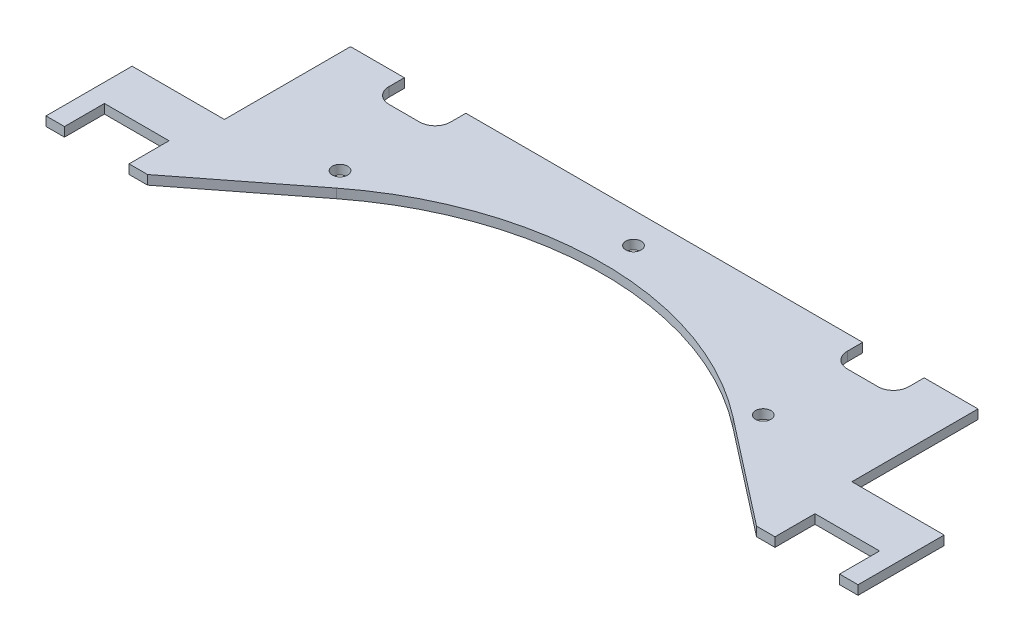
SolidWorks part; units mm, degrees
ref_plane "Face" through (0, 0, 0) normal (0, 0, 1) x (1, 0, 0)
ref_plane "Dessus" through (0, 0, 0) normal (0, 1, 0) x (1, 0, 0)
ref_plane "Droite" through (0, 0, 0) normal (1, 0, 0) x (0, 0, -1)
sketch "Esquisse1" plane through (0, 0, 0) normal (0, 1, 0) x (1, 0, 0)
  line L0 (0, 0) -> (0, 372.8366) construction
  line L1 (0, 0) -> (0, -232.7616) construction
  line L2 (558.5742, 0) -> (-497.8331, 0) construction
  line L3 (-64.4944, 52.8582) -> (-99, 26)
  line L4 (-132, 26) -> (-126, 26)
  line L5 (-132, 26) -> (-132, 54)
  line L6 (-132, 54) -> (-102, 54)
  line L7 (132, 26) -> (132, 54)
  line L8 (-132, 26) -> (-99, 26) construction
  line L9 (64.4944, 52.8582) -> (99, 26)
  line L10 (-79.5, 85) -> (-69.5, 85)
  line L11 (-84.5, 95) -> (-84.5, 90)
  line L12 (-64.5, 95) -> (-64.5, 90)
  line L13 (-64.5, 95) -> (64.5, 95)
  line L14 (-79.5, 90) -> (-69.5, 90) construction
  line L15 (84.5, 95) -> (84.5, 90)
  line L16 (102, 95) -> (84.5, 95)
  line L17 (79.5, 85) -> (69.5, 85)
  line L18 (-102, 54) -> (-102, 95)
  line L19 (-102, 95) -> (-84.5, 95)
  line L20 (-126, 26) -> (-126, 39)
  line L21 (-126, 39) -> (-105, 39)
  line L22 (-105, 39) -> (-105, 26)
  line L23 (-105, 26) -> (-99, 26)
  line L24 (-115.5, 26) -> (-115.5, 39) construction
  line L25 (132, 26) -> (126, 26)
  line L26 (126, 26) -> (126, 39)
  line L27 (126, 39) -> (105, 39)
  line L28 (105, 39) -> (105, 26)
  line L29 (105, 26) -> (99, 26)
  line L30 (132, 54) -> (102, 54)
  line L31 (102, 54) -> (102, 95)
  line L32 (-64.4944, 52.8582) -> (64.4944, 52.8582) construction
  line L33 (-64.4944, 52.8582) -> (-68.794, 58.382) construction
  line L34 (64.5, 95) -> (64.5, 90)
  arc A0 (64.4944, 52.8582) -> (-64.4944, 52.8582) centre (0, -30) ccw
  arc A1 (-84.5, 90) -> (-79.5, 85) centre (-79.5, 90) ccw
  arc A2 (-69.5, 85) -> (-64.5, 90) centre (-69.5, 90) ccw
  arc A3 (84.5, 90) -> (79.5, 85) centre (79.5, 90) cw
  arc A4 (69.5, 85) -> (64.5, 90) centre (69.5, 90) cw
  circle A11 centre (-68.794, 58.382) radius 2.5
  circle A12 centre (68.794, 58.382) radius 2.5
  circle A13 centre (0, 85) radius 2.5
  point P3 (0, 75)
  point P21 (0, 95)
  dimension "D2" = 105
  dimension "D3" = 33
  dimension "D6" = 30
  dimension "D8" = 41
  dimension "D11" = 47.5
  dimension "D19" = 5
  dimension "D21" = 5
  dimension "D1" = 30
  dimension "D4" = 69
  dimension "D5" = 132
  dimension "D7" = 10
  dimension "D9" = 20
  dimension "D10" = 20
  dimension "D12" = 10
  dimension "D14" = 6
  dimension "D15" = 6
  dimension "D16" = 13
  dimension "D20" = 7
  dimension "D22" = 10
extrude "Extrusion1" add sketch "Esquisse1" along normal blind 3
